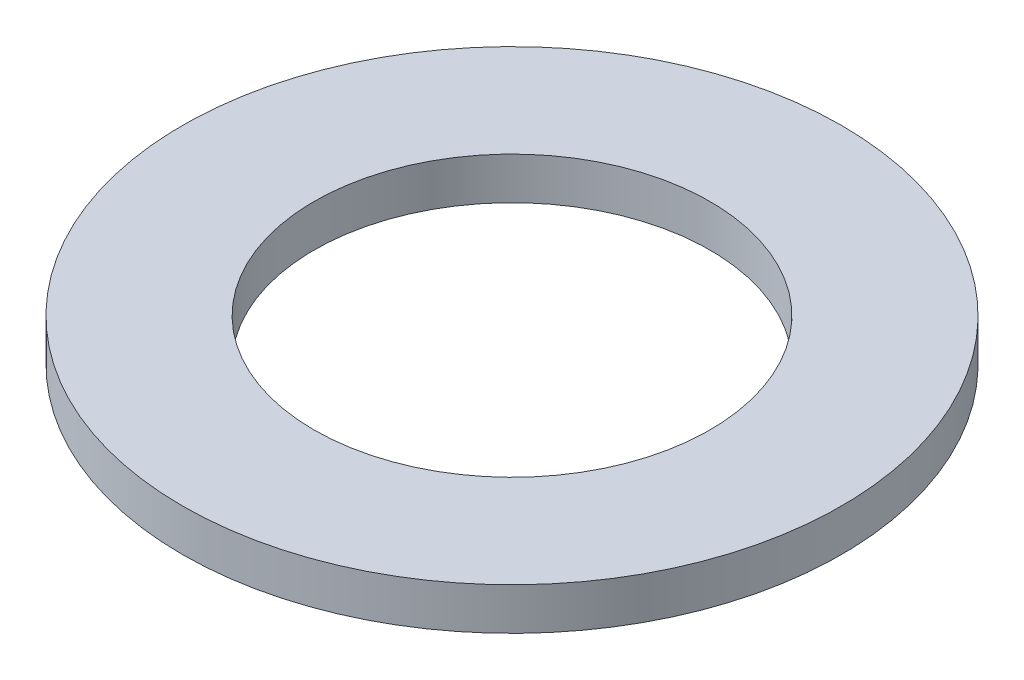
SolidWorks part; units mm, degrees
ref_plane "Front Plane" through (0, 0, 0) normal (0, 0, 1) x (1, 0, 0)
ref_plane "Top Plane" through (0, 0, 0) normal (0, 1, 0) x (1, 0, 0)
ref_plane "Right Plane" through (0, 0, 0) normal (1, 0, 0) x (0, 0, -1)
sketch "Sketch1" plane through (0, 0, 0) normal (0, 1, 0) x (1, 0, 0)
  circle A0 centre (0, 0) radius 2.3876
  circle A1 centre (0, 0) radius 3.9751
  dimension "D1" = 4.7752
  dimension "D2" = 7.9502
extrude "Boss-Extrude1" add sketch "Sketch1" along normal blind 0.508
